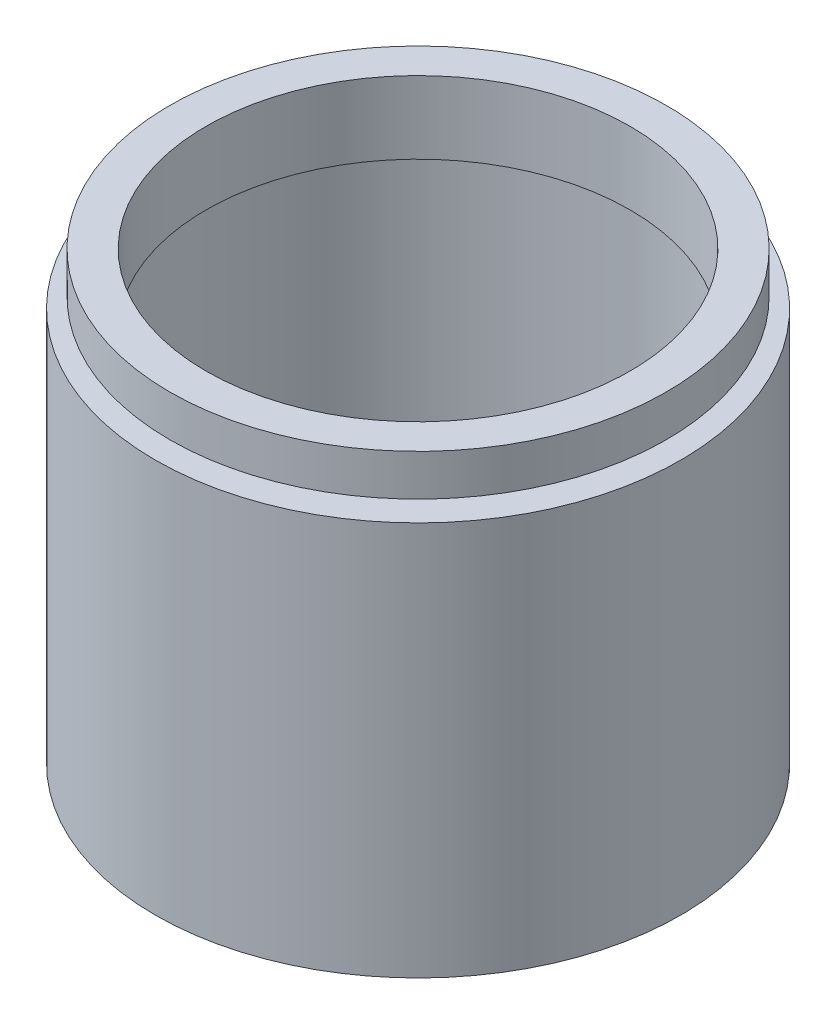
SolidWorks part; units mm, degrees
ref_plane "前视基准面" through (0, 0, 0) normal (0, 0, 1) x (1, 0, 0)
ref_plane "上视基准面" through (0, 0, 0) normal (0, 1, 0) x (1, 0, 0)
ref_plane "右视基准面" through (0, 0, 0) normal (1, 0, 0) x (0, 0, -1)
sketch "草图1" plane through (0, 0, 0) normal (0, 0, 1) x (1, 0, 0)
  line L0 (0, 161.3762) -> (0, 0) construction
  line L1 (141.7365, 0) -> (-131.7984, 0) construction
  line L2 (22.5, 35.1) -> (24, 35.1)
  line L3 (24, 35.1) -> (24, 36.1)
  line L4 (24, 36.1) -> (20.5, 36.1)
  line L5 (20.5, 36.1) -> (20.5, 43.1)
  line L6 (24, 39.1) -> (24, 43.1)
  line L7 (25.4, 38.1) -> (25.4, 0)
  line L8 (25.4, 0) -> (22.5, 0)
  line L9 (22.5, 0) -> (22.5, 5.5)
  line L10 (25.4, 38.1) -> (23.5, 38.1)
  line L11 (20.5, 43.1) -> (24, 43.1)
  line L12 (24, 39.1) -> (22.5, 39.1)
  line L13 (22.5, 39.1) -> (22.5, 38.1)
  line L14 (22.5, 6.5) -> (22.5, 35.1)
  line L15 (22.5, 5.5) -> (23.5, 5.5)
  line L16 (23.5, 5.5) -> (23.5, 6.5)
  line L17 (23.5, 6.5) -> (22.5, 6.5)
  line L18 (22.5, 38.1) -> (23.5, 38.1)
  point P10 (24.45, 38.1)
  dimension "D2" = 38.1
  dimension "D3" = 1
  dimension "D4" = 5.5
  dimension "D5" = 20.5
  dimension "D6" = 24
  dimension "D7" = 22.5
  dimension "D8" = 1
  dimension "D9" = 7
  dimension "D10" = 5
  dimension "D11" = 25.4
  dimension "D12" = 23.5
  dimension "D13" = 1
revolve "旋转1" add sketch "草图1" angle 360 about L0
cosmetic thread "装饰螺纹线1" parameters "D2"=48
cosmetic thread "装饰螺纹线2" parameters "D2"=46
cosmetic thread "装饰螺纹线3" parameters "D2"=42
cosmetic thread "装饰螺纹线5" parameters "D2"=47
